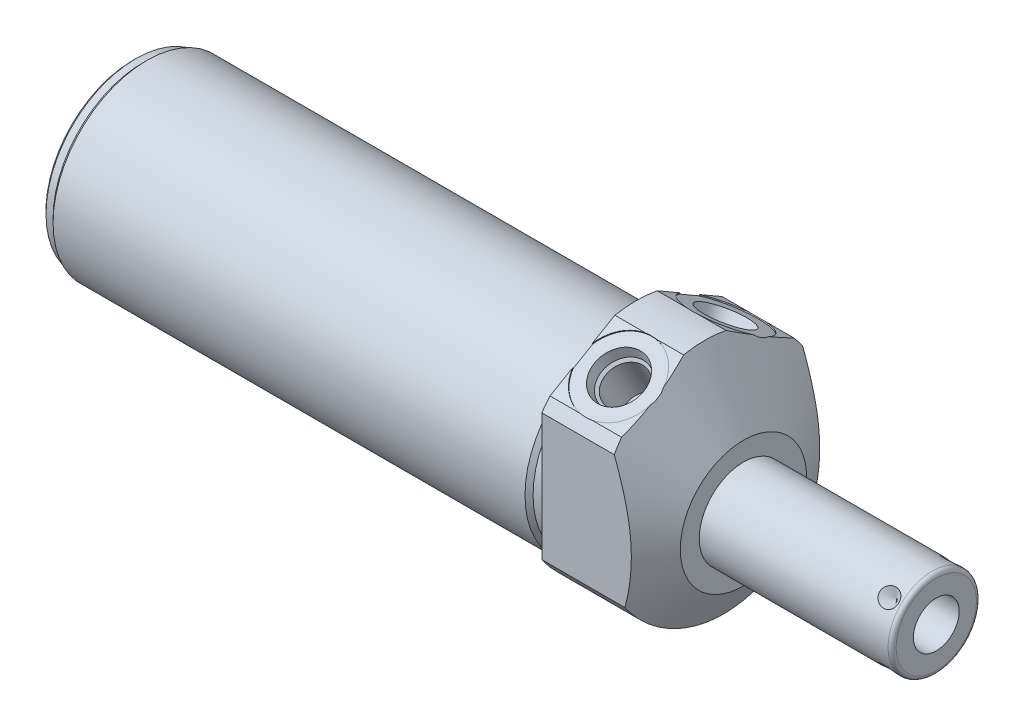
SolidWorks part; units mm, degrees
material "Alloy Steel"
ref_plane "Front Plane" through (0, 0, 0) normal (0, 0, 1) x (1, 0, 0)
ref_plane "Top Plane" through (0, 0, 0) normal (0, 1, 0) x (1, 0, 0)
ref_plane "Right Plane" through (0, 0, 0) normal (1, 0, 0) x (0, 0, -1)
ref_plane "Plane1" through (0, 0, 0) normal (1, 0, 0) x (0, 0, -1)
sketch "Sketch1" plane through (0, 0, 0) normal (1, 0, 0) x (0, 0, -1)
  circle A0 centre (0, 0) radius 28.575
  dimension "D1" = 57.15
extrude "Extrude1" add sketch "Sketch1" along normal blind 27.0002 and the other way blind 126.5428
ref_plane "Plane2" through (0, 0, 0) normal (1, 0, 0) x (0, 0, -1)
sketch "Sketch2" plane through (0, 0, 0) normal (1, 0, 0) x (0, 0, -1)
  line L0 (-25.9842, -4.191) -> (25.9842, -4.191) construction
  circle A0 centre (0, -4.191) radius 23.622
  circle A2 centre (0, 0) radius 28.575
  circle A3 centre (0, 0) radius 28.575
  dimension "D2" = 47.244
  dimension "D1" = 4.191
  dimension "D3" = 0
extrude "Cut-Extrude1" cut sketch "Sketch2" against normal up to next
ref_plane "Plane4" through (0, 0, 0) normal (-1, 0, 0) x (0, 0, 1)
sketch "Sketch4" plane through (0, 0, 0) normal (-1, 0, 0) x (0, 0, 1)
  line L0 (23.6855, -25.6662) -> (23.6855, 17.4761)
  line L1 (23.6855, 17.4761) -> (0, 31.1509)
  line L2 (-23.6855, -25.6662) -> (-23.6855, 17.4761)
  line L3 (-23.6855, 17.4761) -> (0, 31.1509)
  line L4 (0, -31.5613) -> (0, 34.1372) construction
  arc A2 (23.6855, -25.6662) -> (-23.6855, -25.6662) centre (0, 0) ccw
  dimension "D4" = 69.85
  dimension "D1" = 47.371
  dimension "D2" = 30.607
  dimension "D3" = 120
extrude "Cut-Extrude3" cut sketch "Sketch4" against normal up to next
ref_plane "Plane6" through (0, 0, 0) normal (0, 0, 1) x (1, 0, 0)
sketch "Sketch6" plane through (0, 0, 0) normal (0, 0, 1) x (1, 0, 0)
  line L0 (0.7504, 57.15) -> (27.0002, 11.684)
  line L1 (-0.5621, -4.191) -> (28.3127, -4.191) construction
  line L2 (-126.5428, -4.191) -> (0, -4.191) construction
  line L3 (27.0002, 11.684) -> (27.0002, 57.15)
  line L4 (27.0002, 57.15) -> (0.7504, 57.15)
  line L5 (27.0002, 15.9852) -> (27.0002, -15.9852) construction
  dimension "D1" = 60
  dimension "D2" = 31.75
  dimension "D3" = 122.682
revolve "Cut-Revolve2" cut sketch "Sketch6" angle 360 about L1
ref_plane "Plane7" through (9.0932, 23.1369, 13.3727) normal (1, 0, 0) x (0, 0.5, -0.866)
sketch "S2D0002" plane through (9.0932, 23.1369, 13.3727) normal (1, 0, 0) x (0, 0.5, -0.866)
  line L0 (0, 0) -> (6.1849, 0)
  line L1 (6.1849, 0) -> (5.6423, -2.5527)
  line L2 (5.6423, -2.5527) -> (4.9784, -3.2166)
  line L3 (4.9784, -3.2166) -> (4.9784, -13.462)
  line L4 (4.9784, -13.462) -> (0, -13.462)
  line L5 (0, -13.462) -> (0, 0)
  line L6 (0, -14.1351) -> (0, 0.6731) construction
  dimension "D1" = 13.462
revolve "Cut-Revolve3" cut sketch "S2D0002" angle 360 about L6
ref_plane "Plane8" through (9.0932, 23.1369, -13.3727) normal (1, 0, 0) x (0, -0.5, -0.866)
sketch "Sketch8" plane through (9.0932, 23.1369, -13.3727) normal (1, 0, 0) x (0, -0.5, -0.866)
  line L0 (0, 0) -> (6.1849, 0)
  line L1 (6.1849, 0) -> (5.6423, -2.5527)
  line L2 (5.6423, -2.5527) -> (4.9784, -3.2166)
  line L3 (4.9784, -3.2166) -> (4.9784, -13.462)
  line L4 (4.9784, -13.462) -> (0, -13.462)
  line L5 (0, -13.462) -> (0, 0)
  line L6 (0, -14.1351) -> (0, 0.6731) construction
  dimension "D1" = 13.462
revolve "Cut-Revolve4" cut sketch "Sketch8" angle 360 about L6
ref_plane "Plane10" through (0, 0, 0) normal (0, 0, 1) x (1, 0, 0)
sketch "Sketch18" plane through (0, 23.3632, 13.4887) normal (0, 0.866, 0.5) x (1, 0, 0)
  circle A0 centre (9.0932, -0.0127) radius 9.525
  dimension "D1" = 19.05
extrude "Cut-Extrude4" cut sketch "Sketch18" against normal blind 0.254
sketch "Sketch19" plane through (0, 23.3632, -13.4887) normal (0, 0.866, -0.5) x (1, 0, 0)
  circle A0 centre (9.0932, 0.0127) radius 9.525
  circle A1 centre (9.0932, 0.0127) radius 6.1849 construction
  dimension "D1" = 19.05
extrude "Cut-Extrude5" cut sketch "Sketch19" against normal blind 0.254
sketch "Sketch10" plane through (0, 0, 0) normal (0, 0, 1) x (1, 0, 0)
  line L0 (0, 19.431) -> (0, 18.415)
  line L1 (0, 18.415) -> (-3.302, 18.415)
  line L2 (-3.302, 18.415) -> (-4.318, 19.431)
  line L3 (-4.5339, -4.191) -> (0.2159, -4.191) construction
  line L4 (0, 19.431) -> (-4.318, 19.431)
  line L5 (-126.5428, -4.191) -> (0, -4.191) construction
  line L6 (0, 19.431) -> (-126.5428, 19.431) construction
  line L7 (0, 21.9392) -> (0, 18.6529) construction
  dimension "D1" = 45.212
  dimension "D2" = 45
  dimension "D3" = 3.302
revolve "Cut-Revolve6" cut sketch "Sketch10" angle 360 about L3
ref_plane "Plane12" through (0, 0, 0) normal (0, 0, 1) x (1, 0, 0)
sketch "Sketch12" plane through (0, 0, 0) normal (0, 0, 1) x (1, 0, 0)
  line L0 (-126.5428, 19.431) -> (-126.5428, 18.415)
  line L1 (-126.5428, 18.415) -> (-124.0028, 18.415)
  line L2 (-124.0028, 18.415) -> (-122.9868, 19.431)
  line L3 (-84.3026, -4.191) -> (-80.391, -4.191) construction
  line L4 (-126.5428, 19.431) -> (-122.9868, 19.431)
  line L5 (-126.5428, -4.191) -> (-4.318, -4.191) construction
  line L6 (-4.318, 19.431) -> (-126.5428, 19.431) construction
  line L7 (-126.5428, 19.431) -> (-126.5428, -27.813) construction
  dimension "D1" = 45.212
  dimension "D2" = 45
  dimension "D3" = 2.54
revolve "Cut-Revolve8" cut sketch "Sketch12" angle 360 about L3
chamfer "Chamfer1" distance 0.762 angle 45 1 edges at (-126.5428, -4.191, 22.606)
ref_plane "Plane13" through (0, 0, 0) normal (0, 0, 1) x (0, -1, 0)
sketch "Sketch13" plane through (0, 0, 0) normal (0, 0, 1) x (0, -1, 0)
  line L0 (4.191, 27.0002) -> (4.191, 75.4888)
  line L1 (4.191, 75.4888) -> (14.2875, 75.4888)
  line L2 (15.3035, 74.4728) -> (15.3035, 27.0002)
  line L3 (15.3035, 27.0002) -> (4.191, 27.0002)
  line L4 (4.191, 25.1066) -> (4.191, 66.7652) construction
  line L5 (4.191, -122.9868) -> (4.191, -4.318) construction
  line L6 (20.066, 27.0002) -> (-11.684, 27.0002) construction
  line L7 (-18.415, 0) -> (26.797, 0) construction
  arc A0 (15.3035, 74.4728) -> (14.2875, 75.4888) centre (14.2875, 74.4728) ccw
  dimension "D3" = 1.016
  dimension "D1" = 22.225
  dimension "D2" = 75.4888
revolve "Revolve1" add sketch "Sketch13" angle 360 about L4
ref_plane "Plane14" through (64.8716, -9.9441, 0) normal (0, 0, 1) x (0, -1, 0)
sketch "S2D0001" plane through (64.8716, -9.9441, 0) normal (0, 0, 1) x (0, -1, 0)
  line L0 (0, 10.6172) -> (0, -6.4008)
  line L1 (0, -6.4008) -> (-5.7531, -9.8576)
  line L2 (0, 10.6172) -> (-5.7531, 10.6172)
  line L3 (-5.7531, 10.6172) -> (-5.7531, -9.8576)
  line L4 (-5.7531, -21.4986) -> (-5.7531, 1.0237) construction
  line L5 (-5.7531, 9.6012) -> (-5.7531, -37.8714) construction
  line L6 (4.3434, 10.6172) -> (-15.8496, 10.6172) construction
  dimension "D1" = 11.5062
  dimension "D2" = 59
  dimension "D3" = 17.018
revolve "Cut-Revolve9" cut sketch "S2D0001" angle 360 about L4
ref_plane "Plane16" through (60.9092, -15.3035, 0) normal (0, 0, 1) x (-1, 0, 0)
ref_plane "Plane17" through (0, -2.0955, -2.0955) normal (0, 0.7071, 0.7071) x (-1, 0, 0)
sketch "Sketch16" plane through (60.9092, 3.6667, -7.8577) normal (0, -0.7071, -0.7071) x (-1, 0, 0)
  line L0 (-10.6172, 0) -> (-8.2042, 0)
  line L1 (-8.2042, 0) -> (-10.6172, -2.413)
  line L2 (-10.6172, 0) -> (-10.6172, -2.413)
  line L3 (-10.6172, -4.4865) -> (-10.6172, 0.1207) construction
  line L4 (-14.5796, -1.016) -> (-14.5796, -21.209) construction
  line L5 (33.909, 0) -> (-13.5636, 0) construction
  dimension "D1" = 45
  dimension "D2" = 3.9624
  dimension "D3" = 4.826
revolve "Cut-Revolve10" cut sketch "Sketch16" angle 360 about L3
pattern_circular "CirPattern1" count 4 over 360 about axis through (25.1066, -4.191, 0) along (-1, 0, 0) of "Cut-Revolve10"
